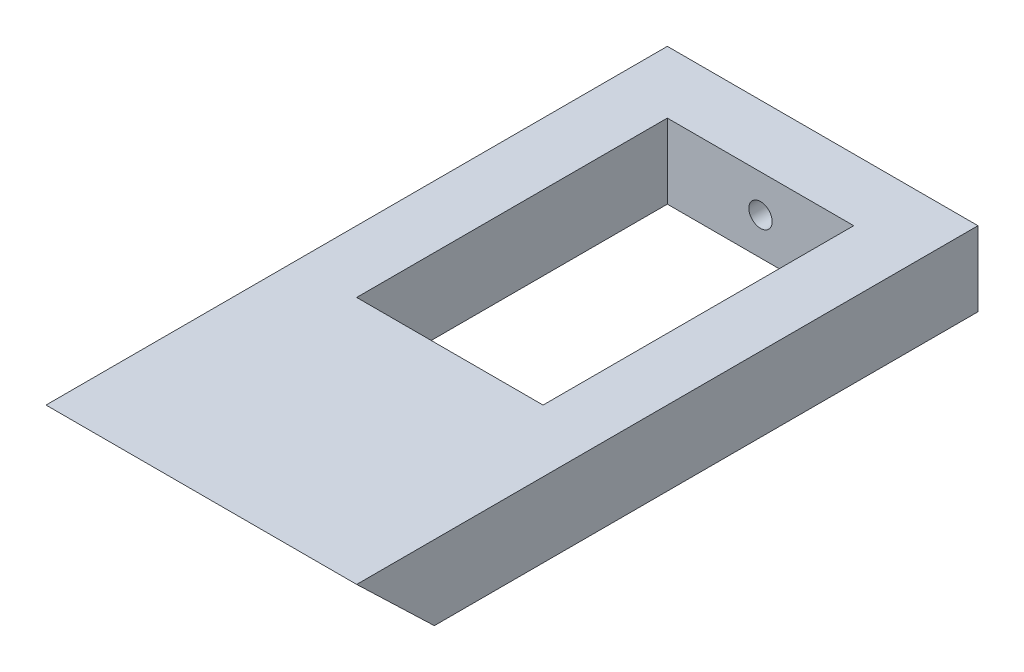
SolidWorks part; units mm, degrees
ref_plane "Front Plane" through (0, 0, 0) normal (0, 0, 1) x (1, 0, 0)
ref_plane "Top Plane" through (0, 0, 0) normal (0, 1, 0) x (1, 0, 0)
ref_plane "Right Plane" through (0, 0, 0) normal (1, 0, 0) x (0, 0, -1)
sketch "Sketch1" plane through (0, 0, 0) normal (0, 1, 0) x (1, 0, 0)
  line L1 (-12.7, -25.4) -> (12.7, -25.4)
  line L2 (-12.7, -25.4) -> (-12.7, 25.4)
  line L3 (-12.7, 25.4) -> (12.7, 25.4)
  line L4 (12.7, -25.4) -> (12.7, 25.4)
  line L5 (-12.7, -25.4) -> (12.7, 25.4) construction
  line L6 (-12.7, 25.4) -> (12.7, -25.4) construction
  point P0 (0, 0)
  dimension "D1" = 25.4
  dimension "D2" = 50.8
extrude "Boss-Extrude1" add sketch "Sketch1" along normal blind 6.096
sketch "Sketch3" plane through (12.7, 0, 0) normal (1, 0, 0) x (0, 0, -1)
  line L0 (-25.4, 6.096) -> (-25.4, 0)
  line L1 (-25.4, 0) -> (-19.05, 0)
  line L2 (-25.4, 0) -> (25.4, 0) construction
  line L3 (-19.05, 0) -> (-25.4, 6.096)
  dimension "D1" = 6.35
extrude "Cut-Extrude2" cut sketch "Sketch3" against normal through all
sketch "Sketch4" plane through (0, 0, 0) normal (0, -1, 0) x (1, 0, 0)
  line L0 (12.7, -25.4) -> (-12.7, -25.4) construction
  line L1 (-7.62, -20.32) -> (7.62, -20.32)
  line L2 (-7.62, -20.32) -> (-7.62, 5.08)
  line L3 (-7.62, 5.08) -> (7.62, 5.08)
  line L4 (7.62, -20.32) -> (7.62, 5.08)
  line L5 (-12.7, -25.4) -> (-12.7, 19.05) construction
  line L6 (12.7, 19.05) -> (12.7, -25.4) construction
  dimension "D1" = 5.08
  dimension "D2" = 5.08
  dimension "D3" = 5.08
  dimension "D4" = 25.4
extrude "Cut-Extrude3" cut sketch "Sketch4" against normal through all
sketch "Sketch5" plane through (0, 0, 5.08) normal (0, 0, -1) x (-1, 0, 0)
  line L0 (-3.81, 3.302) -> (3.81, 3.302) construction
  line L1 (-7.62, 0) -> (7.62, 0) construction
  circle A0 centre (-3.81, 3.302) radius 2.286
  circle A1 centre (3.81, 3.302) radius 2.286
  point P3 (0, 3.302)
  dimension "D1" = 4.572
  dimension "D2" = 4.572
  dimension "D3" = 7.62
  dimension "D4" = 3.302
extrude "Cut-Extrude4" cut sketch "Sketch5" against normal blind 2.54
sketch "Sketch6" plane through (0, 0, -25.4) normal (0, 0, -1) x (-1, 0, 0)
  line L0 (0, 0) -> (0, 6.096) construction
  line L1 (-12.7, 0) -> (12.7, 0) construction
  line L2 (-12.7, 6.096) -> (12.7, 6.096) construction
  circle A0 centre (0, 3.048) radius 0.9525
  dimension "D1" = 1.905
extrude "Cut-Extrude5" cut sketch "Sketch6" against normal up to next
